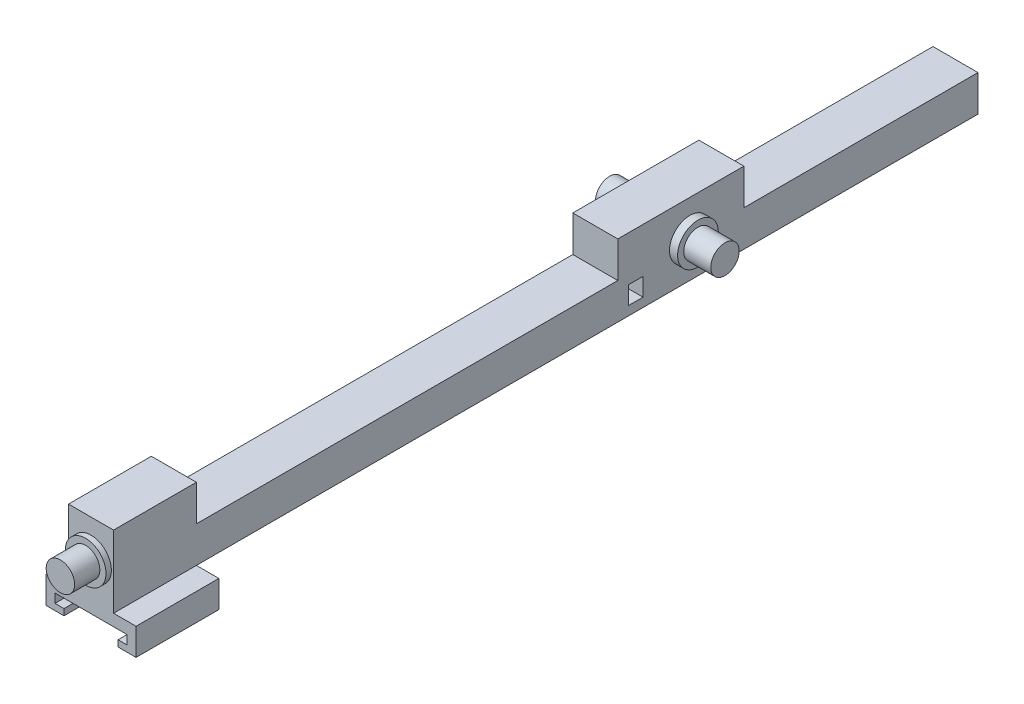
SolidWorks part; units mm, degrees
material "6061 Alloy"
ref_plane "Front Plane" through (0, 0, 0) normal (0, 0, 1) x (1, 0, 0)
ref_plane "Top Plane" through (0, 0, 0) normal (0, 1, 0) x (1, 0, 0)
ref_plane "Right Plane" through (0, 0, 0) normal (1, 0, 0) x (0, 0, -1)
sketch "Sketch1" plane through (0, 0, 0) normal (0, 1, 0) x (1, 0, 0)
  line L0 (0, 0) -> (6.25, 0) construction
  line L1 (-6.25, 80) -> (6.25, 80)
  line L2 (-6.25, 80) -> (-6.25, -160)
  line L3 (-6.25, -160) -> (6.25, -160)
  line L4 (6.25, -160) -> (6.25, 0)
  line L5 (6.25, 0) -> (6.25, 80)
  point P0 (0, 0)
  dimension "D1" = 12.5
  dimension "D2" = 6.25
  dimension "D3" = 160
  dimension "D4" = 80
extrude "Boss-Extrude1" add sketch "Sketch1" along normal blind 20
sketch "Sketch2" plane through (0, 0, 160) normal (0, 0, 1) x (1, 0, 0)
  line L0 (0, 0) -> (0, 10) construction
  line L1 (-6.25, 0) -> (6.25, 0) construction
  circle A0 centre (0, 10) radius 5.65
  dimension "D2" = 11.3
  dimension "D1" = 10
extrude "Boss-Extrude2" add sketch "Sketch2" along normal blind 1.5
sketch "Sketch3" plane through (0, 0, 161.5) normal (0, 0, 1) x (1, 0, 0)
  line L0 (0, 0) -> (0, 10) construction
  circle A0 centre (0, 10) radius 3.95
  dimension "D1" = 7.9
extrude "Boss-Extrude3" add sketch "Sketch3" along normal blind 7
sketch "Sketch4" plane through (-6.25, 0, 0) normal (-1, 0, 0) x (0, 0, 1)
  line L0 (160, 10) -> (0, 10) construction
  line L1 (160, 20) -> (160, 0) construction
  circle A0 centre (0, 10) radius 5.65
  dimension "D2" = 11.3
  dimension "D1" = 160
extrude "Boss-Extrude4" add sketch "Sketch4" along normal blind 2.25
sketch "Sketch5" plane through (-8.5, 0, 0) normal (-1, 0, 0) x (0, 0, 1)
  circle A0 centre (0, 10) radius 3.95
  dimension "D1" = 7.9
extrude "Boss-Extrude5" add sketch "Sketch5" along normal blind 7.5
mirror "Mirror1" about plane through (0, 0, 0) normal (1, 0, 0) of "Boss-Extrude5", "Boss-Extrude4"
sketch "Sketch9" plane through (0, 0, 160) normal (0, 0, 1) x (1, 0, 0)
  line L8 (-12.5, 0) -> (12.5, 0)
  line L10 (12.5, 0) -> (12.5, -7.5)
  line L11 (-12.5, 0) -> (-12.5, -7.5)
  line L12 (-12.5, -7.5) -> (12.5, -7.5)
  point P3 (0, 0)
  dimension "D1" = 25
  dimension "D2" = 7.5
  dimension "D3" = 7.5
extrude "Boss-Extrude8" add sketch "Sketch9" against normal blind 23
sketch "Sketch10" plane through (0, 0, 160) normal (0, 0, 1) x (1, 0, 0)
  line L0 (0, -7.5) -> (0, -6) construction
  line L1 (-12.5, -7.5) -> (12.5, -7.5) construction
  line L2 (0, 0) -> (0, -3.25) construction
  line L4 (-10, -5.75) -> (-10, -3.25)
  line L5 (-10, -3.25) -> (10, -3.25)
  line L6 (10, -5.75) -> (10, -3.25)
  line L7 (-10, -5.75) -> (-7.5, -5.75)
  line L8 (10, -5.75) -> (7.5, -5.75)
  line L9 (-7.5, -5.75) -> (-7.5, -7.5)
  line L10 (-7.5, -7.5) -> (7.5, -7.5)
  line L11 (7.5, -7.5) -> (7.5, -5.75)
  dimension "D1" = 1.5
  dimension "D2" = 20
  dimension "D3" = 2.5
  dimension "D4" = 3.25
  dimension "D5" = 2.5
  dimension "D6" = 2.5
  dimension "D7" = 2.5
extrude "Cut-Extrude1" cut sketch "Sketch10" against normal blind 20
sketch "Sketch12" plane through (-6.25, 0, 0) normal (-1, 0, 0) x (0, 0, 1)
  line L0 (0, 10) -> (13, 10) construction
  line L1 (13, 10) -> (13, 7.5) construction
  line L3 (13, 7.5) -> (17, 7.5)
  line L4 (13, 7.5) -> (13, 2.5)
  line L5 (13, 2.5) -> (17, 2.5)
  line L6 (17, 7.5) -> (17, 2.5)
  dimension "D1" = 13
  dimension "D2" = 2.5
  dimension "D3" = 5
  dimension "D4" = 4
extrude "Cut-Extrude2" cut sketch "Sketch12" against normal up to next
sketch "Sketch14" plane through (-6.25, 0, 0) normal (-1, 0, 0) x (0, 0, 1)
  line L0 (0, 10) -> (-15, 10) construction
  line L1 (137, 0) -> (137, 20) construction
  line L2 (-80, 20) -> (-15, 20)
  line L3 (-80, 20) -> (-80, 10)
  line L4 (-80, 10) -> (-15, 10)
  line L5 (-15, 20) -> (-15, 10)
  line L6 (-80, 20) -> (160, 20) construction
  line L7 (0, 10) -> (20, 10) construction
  line L9 (137, 20) -> (20, 20)
  line L10 (137, 20) -> (137, 10)
  line L11 (137, 10) -> (20, 10)
  line L12 (20, 20) -> (20, 10)
  dimension "D1" = 15
  dimension "D2" = 10
  dimension "D3" = 20
  dimension "D4" = 10
extrude "Cut-Extrude3" cut sketch "Sketch14" against normal up to next
equation "\"Front Length\"= 16cm"
equation "\"Back Length\"= 8cm"
equation "\"D1@Sketch4\"=\"Front Length\""
equation "\"D3@Sketch1\"=\"Front Length\""
equation "\"D4@Sketch1\"=\"Back Length\""
equation "\"D1@Fillet19\"=\"Fillet Radius\""
equation "\"Fillet Radius\"= .15cm"
